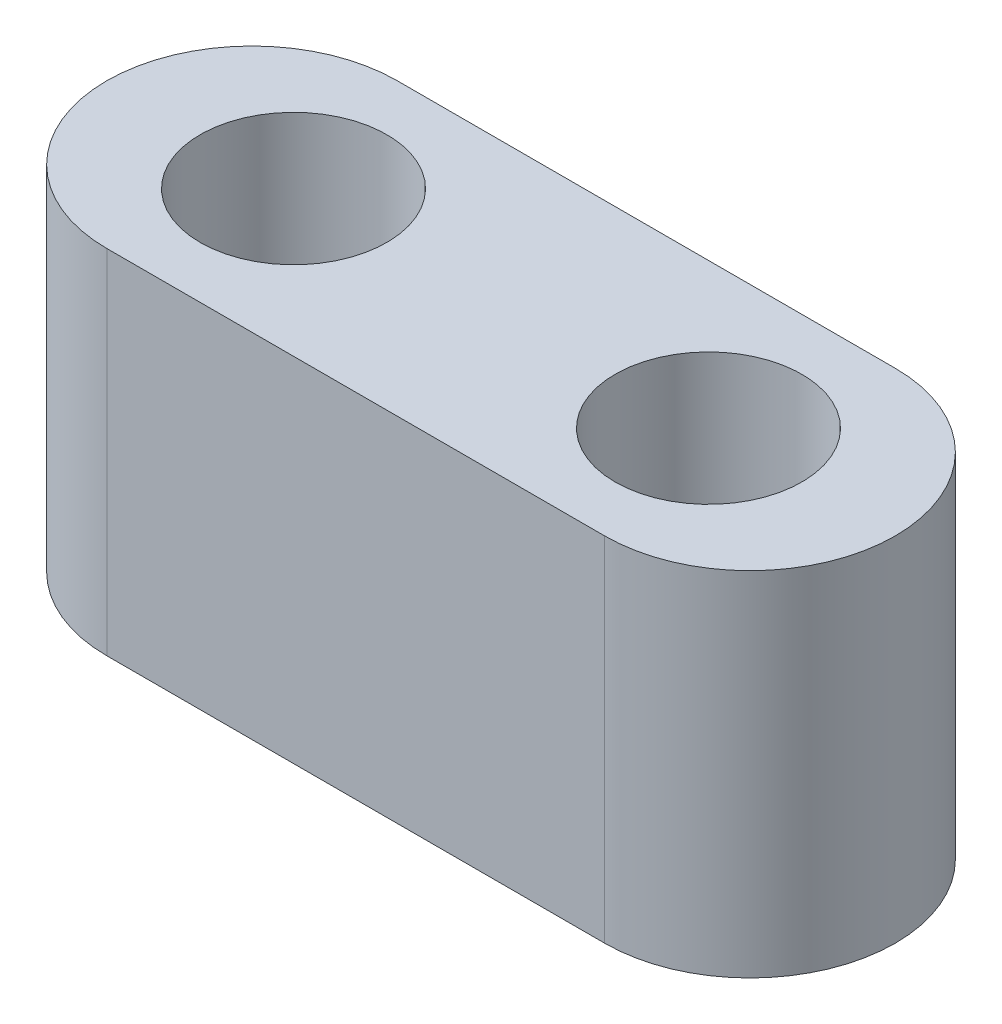
SolidWorks part; units mm, degrees
ref_plane "Płaszczyzna przednia" through (0, 0, 0) normal (0, 0, 1) x (1, 0, 0)
ref_plane "Płaszczyzna górna" through (0, 0, 0) normal (0, 1, 0) x (1, 0, 0)
ref_plane "Płaszczyzna prawa" through (0, 0, 0) normal (1, 0, 0) x (0, 0, -1)
sketch "Sketch1" plane through (0, 0, 0) normal (0, 1, 0) x (1, 0, 0)
  line L0 (0, 0) -> (5, 0) construction
  line L1 (-6, -3.5) -> (6, -3.5)
  line L3 (-6, 3.5) -> (6, 3.5)
  line L7 (0, 0) -> (-5, 0) construction
  line L8 (-5, 0) -> (-6, 0) construction
  line L9 (5, 0) -> (6, 0) construction
  circle A0 centre (5, 0) radius 2.25
  circle A1 centre (-5, 0) radius 2.25
  arc A2 (-6, 3.5) -> (-6, -3.5) centre (-6, 0) ccw
  arc A3 (6, -3.5) -> (6, 3.5) centre (6, 0) ccw
  point P0 (0, 0)
  dimension "D3" = 5
  dimension "D4" = 5
  dimension "D5" = 10
extrude "Boss-Extrude1" add sketch "Sketch1" along normal blind 8.5
